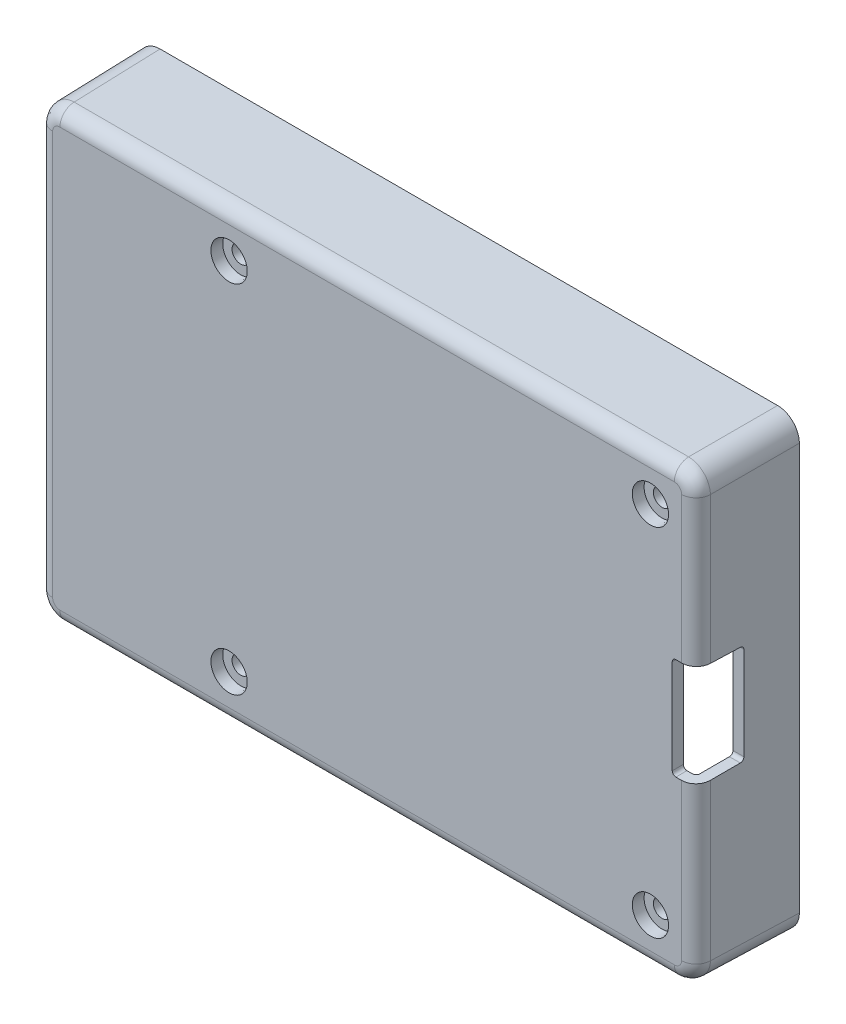
SolidWorks part; units mm, degrees
ref_plane "Front" through (0, 0, 0) normal (0, 0, 1) x (1, 0, 0)
ref_plane "Top" through (0, 0, 0) normal (0, 1, 0) x (1, 0, 0)
ref_plane "Right" through (0, 0, 0) normal (1, 0, 0) x (0, 0, -1)
sketch "Sketch1" plane through (0, 0, 0) normal (0, 0, 1) x (1, 0, 0)
  circle A0 centre (-19, 24.5) radius 3.5
  circle A1 centre (39, 24.5) radius 3.5
  circle A2 centre (39, -24.5) radius 3.5
  circle A3 centre (-19, -24.5) radius 3.5
  dimension "D1" = 7
extrude "Standoffs" add sketch "Sketch1" along normal blind 6 draft 1 draft outward yes
sketch "Sketch2" plane through (0, 0, 6) normal (0, 0, 1) x (1, 0, 0)
  line L0 (40, -28) -> (-40, -28) construction
  line L1 (-45.5, 31) -> (45.5, 31)
  line L2 (-45.5, 31) -> (-45.5, -31)
  line L3 (-45.5, -31) -> (45.5, -31)
  line L4 (45.5, 31) -> (45.5, -31)
  line L5 (-45.5, 31) -> (45.5, -31) construction
  line L6 (-45.5, -31) -> (45.5, 31) construction
  line L7 (42.5, 25.5) -> (42.5, -25.5) construction
  point P0 (0, 0)
  dimension "D1" = 3
  dimension "D2" = 3
extrude "Base" add sketch "Sketch2" against normal blind 1.5
sketch "Sketch3" plane through (0, 0, 4.5) normal (0, 0, -1) x (-1, 0, 0)
  line L0 (-44, 29.5) -> (-44, -29.5)
  line L1 (-44, -29.5) -> (44, -29.5)
  line L2 (44, -29.5) -> (44, 29.5)
  line L3 (44, 29.5) -> (-44, 29.5)
  line L4 (-45.5, 31) -> (-45.5, -31)
  line L5 (-45.5, -31) -> (45.5, -31)
  line L6 (45.5, -31) -> (45.5, 31)
  line L7 (45.5, 31) -> (-45.5, 31)
  line L8 (-45.5, 31) -> (-45.5, -31)
  line L9 (-45.5, -31) -> (45.5, -31)
  line L10 (45.5, -31) -> (45.5, 31)
  line L11 (45.5, 31) -> (-45.5, 31)
  dimension "D1" = 0
  dimension "D2" = 1.5
extrude "Walls " add sketch "Sketch3" along normal blind 12.5
hole_wizard "CBORE for M2 Pan Head Machine Screw1" positions "Sketch4" profile "Sketch5" counterbore size "M2" standard "ANSI Metric" end condition through all
sketch "Sketch4" plane through (0, 0, 6) normal (0, 0, 1) x (1, 0, 0)
  point P0 (39, -24.5)
  point P2 (-19, 24.5)
  point P4 (39, 24.5)
  point P6 (-19, -24.5)
  point P9 (-19, 24.5)
  point P11 (39, 24.5)
  point P13 (39, -24.5)
  point P15 (-19, -24.5)
sketch "Sketch5" plane through (39, -24.5, 6) normal (1, 0, 0) x (0, -1, 0)
  line L0 (0, 0) -> (0, 14)
  line L1 (0, 14) -> (1.2, 14)
  line L3 (1.2, 14) -> (1.2, 1.6)
  line L4 (1.2, 1.6) -> (2.5, 1.6)
  line L5 (2.5, 1.6) -> (2.5, 0)
  line L7 (2.5, 0) -> (0, 0)
  line L11 (0, -6.35) -> (0, 107.95) construction
  dimension "Thru Hole Dia." = 2.4
  dimension "Thru Hole Depth" = 14
  dimension "C'Bore Dia." = 5
  dimension "C'Bore Depth" = 1.6
sketch "Sketch7" plane through (0, 0, 0) normal (0, 1, 0) x (1, 0, 0)
  line L0 (10.2, 7.8) -> (10.2, 1.72) construction
  line L1 (12.32, 7.8) -> (8.08, 7.8) construction
  line L2 (15.85, 1.72) -> (4.55, 1.72) construction
  line L3 (40, 1.3) -> (-40, 1.3) construction
  line L4 (18.2, 8.22) -> (2.2, 8.22)
  line L5 (18.2, 8.22) -> (18.2, 1.3)
  line L6 (18.2, 1.3) -> (2.2, 1.3)
  line L7 (2.2, 8.22) -> (2.2, 1.3)
  line L8 (18.2, 8.22) -> (2.2, 1.3) construction
  line L9 (18.2, 1.3) -> (2.2, 8.22) construction
  line L10 (2.7, 6.1) -> (2.7, 5.4) construction
  line L11 (31.75, 4.1294) -> (31.75, 1.44) construction
  line L12 (28.75, 4.1294) -> (34.75, 4.1294) construction
  line L13 (31.635, 1.44) -> (31.865, 1.44) construction
  line L14 (27.51, 4.6294) -> (27.51, 8)
  line L15 (35.99, 0.94) -> (27.51, 0.94)
  line L16 (35.99, 0.94) -> (35.99, 4.6294)
  line L17 (35.99, 4.6294) -> (27.51, 4.6294)
  line L18 (27.51, 0.94) -> (27.51, 4.6294)
  line L19 (35.99, 0.94) -> (27.51, 4.6294) construction
  line L20 (35.99, 4.6294) -> (27.51, 0.94) construction
  line L21 (-45.5, 8) -> (45.5, 8) construction
  line L22 (27.51, 8) -> (35.99, 8)
  line L23 (35.99, 8) -> (35.99, 4.6294)
  line L24 (-14.4, 4.3) -> (-14.4646, 8)
  line L25 (-14.4646, 8) -> (-7.3354, 8)
  line L26 (-7.3354, 8) -> (-7.4, 4.3)
  line L27 (-10.9, 4.3) -> (-10.9, 8) construction
  circle A0 centre (-10.9, 4.3) radius 3.5
  arc A1 (-9.9633, 7.15) -> (-11.8367, 7.15) centre (-10.9, 4.3) ccw construction
  point P12 (10.2, 4.76)
  point P27 (31.75, 2.7847)
  point P40 (35.99, 8)
  dimension "D1" = 0.5
  dimension "D2" = 0.5
  dimension "D3" = 0.5
  dimension "D4" = 0.5
  dimension "D5" = 1
extrude "Side Ports " cut sketch "Sketch7" against normal through all contours A0 | A0 L26 L25 L24 | L4 L7 L6 L5 | L23 L22 L14 L17 | L18 L15 L16 L17
sketch "Sketch6" plane through (0, 0, 0) normal (1, 0, 0) x (0, 0, -1)
  line L4 (15.8, -8.696) -> (1.6, -8.696)
  line L5 (1.6, -8.696) -> (1.6, -26)
  line L6 (1.6, -26) -> (15.8, -26)
  line L7 (15.8, -26) -> (15.8, -8.696)
  line L8 (15.8, -8.696) -> (1.6, -8.696)
  line L9 (1.6, -8.696) -> (1.6, -26)
  line L10 (1.6, -26) -> (15.8, -26)
  line L11 (15.8, -26) -> (15.8, -8.696)
  line L12 (0.81, -6.14) -> (17.3, -6.14)
  line L13 (0.81, 8.64) -> (0.81, -6.14)
  line L14 (17.3, 8.64) -> (0.81, 8.64)
  line L15 (17.3, -6.14) -> (17.3, 8.64)
  line L16 (0.81, -6.14) -> (17.3, -6.14)
  line L17 (0.81, 8.64) -> (0.81, -6.14)
  line L18 (17.3, 8.64) -> (0.81, 8.64)
  line L19 (17.3, -6.14) -> (17.3, 8.64)
  line L20 (0.81, 11.46) -> (17.3, 11.46)
  line L21 (0.81, 26.24) -> (0.81, 11.46)
  line L22 (17.3, 26.24) -> (0.81, 26.24)
  line L23 (17.3, 11.46) -> (17.3, 26.24)
  line L24 (0.81, 11.46) -> (17.3, 11.46)
  line L25 (0.81, 26.24) -> (0.81, 11.46)
  line L26 (17.3, 26.24) -> (0.81, 26.24)
  line L27 (17.3, 11.46) -> (17.3, 26.24)
  dimension "D1" = 0
  dimension "D2" = 0
  dimension "D3" = 0
extrude "Ethernet Cuts" cut sketch "Sketch6" against normal through all
draft "Draft2" type of draft neutral plane draft angle 1 faces to draft 4 face at (-44, 0.688, -3.84) face at (0, 29.5, -1.75) face at (44, 0, -1.75) face at (7.7625, -29.5, -4.0363) neutral plane through (0, 0, -8) neutral plane normal (0, 0, -1) parameters "D1"=1
draft "Draft1" type of draft neutral plane draft angle 1 faces to draft 4 face at (-45.5, 0.688, -3.6525) face at (0, 31, -1) face at (45.5, 0, -1) face at (7.7625, -31, -3.8488) neutral plane through (0, 0, -8) neutral plane normal (0, 0, -1) reverse direction yes parameters "D1"=1
fillet "Fillet1" radius 3 4 edges at (-45.3778, -30.8778, -1) (45.3778, -30.8778, -1) (45.3778, 30.8778, -1) (-45.3778, 30.8778, -1)
fillet "Fillet2" radius 1.5 4 edges at (-43.8909, -29.3909, -1.75) (-43.8909, 29.3909, -1.75) (43.8909, 29.3909, -1.75) (43.8909, -29.3909, -1.75)
fillet "Fillet3" radius 2 8 edges at (44.3771, 29.8771, 6) (45.2556, 0, 6) (44.3771, -29.8771, 6) (0, -30.7556, 6) (-44.3771, -29.8771, 6) (-45.2556, 0, 6) (-44.3771, 29.8771, 6) (0, 30.7556, 6)
fillet "Fillet4" radius 0.5 12 edges at (-15.4215, 24.5, 4.5) (42.5785, 24.5, 4.5) (42.5785, -24.5, 4.5) (-15.4215, -24.5, 4.5) (43.3426, -28.8426, 4.5) (43.7818, 0, 4.5) (43.3426, 28.8426, 4.5) (0, 29.2818, 4.5) (-43.3426, 28.8426, 4.5) (-43.7818, 0, 4.5) (-43.3426, -28.8426, 4.5) (0, -29.2818, 4.5)
sketch "Sketch8" plane through (0, 0, 0) normal (1, 0, 0) x (0, 0, -1)
  line L0 (-1.3, 0.7) -> (0, 0.7) construction
  line L1 (-1.3, 7.2) -> (-1.3, -5.8) construction
  line L2 (-1.3, 7.2) -> (0, 7.2) construction
  line L3 (-1.8, -6.3) -> (0.5, -6.3)
  line L4 (-1.8, -6.3) -> (-1.8, 7.7)
  line L5 (-1.8, 7.7) -> (0.5, 7.7)
  line L6 (0.5, -6.3) -> (0.5, 7.7)
  line L7 (-1.8, -6.3) -> (0.5, 7.7) construction
  line L8 (-1.8, 7.7) -> (0.5, -6.3) construction
  line L9 (-1.8, -6.3) -> (-6, -6.3)
  line L10 (-6, -30.7556) -> (-6, 30.7556) construction
  line L11 (-6, -6.3) -> (-6, 7.7)
  line L12 (-6, 7.7) -> (-1.8, 7.7)
  point P5 (-0.65, 0.7)
  dimension "D1" = 0.5
  dimension "D2" = 0.5
extrude "SD Card Cut " cut sketch "Sketch8" along normal through all from offset 42 contours L3 L6 L5 L4 | L12 L11 L9 L4
draft "Draft3" type of draft neutral plane draft angle 1 faces to draft 10 face at (2.2, -30.1915, -4.65) face at (27.51, -30.1884, -4.47) face at (18.2, -30.1915, -4.65) face at (35.99, -30.1884, -4.47) face at (-44.6872, 11.46, -4.405) face at (-44.6872, -6.14, -4.405) face at (-44.6941, -26, -4.8) face at (-44.6872, 8.64, -4.405) face at (-44.6941, -8.696, -4.8) face at (-44.6872, 26.24, -4.405) neutral plane through (0, 0, -8) neutral plane normal (0, 0, -1) parameters "D1"=1
draft "Draft4" type of draft neutral plane draft angle 1 faces to draft 3 face at (42, 0.7, 5.25) face at (43.6752, -6.3, 3.5694) face at (43.6752, 7.7, 3.5694) neutral plane through (-19, 24.5, 6) neutral plane normal (0, 0, 1) parameters "D1"=1
draft "Draft5" type of draft neutral plane draft angle 1 faces to draft 4 face at (41.5, 24.5, 4.4) face at (-16.5, -24.5, 4.4) face at (-16.5, 24.5, 4.4) face at (41.5, -24.5, 4.4) neutral plane through (-19, 24.5, 6) neutral plane normal (0, 0, 1) parameters "D1"=1
fillet "Fillet5" radius 1 4 edges at (27.6332, -30.1268, -0.94) (2.3169, -30.1331, -1.3) (18.0831, -30.1331, -1.3) (35.8668, -30.1268, -0.94)
fillet "Fillet6" radius 0.5 10 edges at (44.6191, -6.1865, -0.5) (42.0131, -6.2869, 5.25) (42.0131, 7.6869, 5.25) (44.6191, 7.5865, -0.5) (-44.6245, 11.5855, -0.81) (-44.6245, -6.0145, -0.81) (-44.6383, -25.8883, -1.6) (-44.6383, -8.8077, -1.6) (-44.6245, 8.5145, -0.81) (-44.6245, 26.1145, -0.81)
